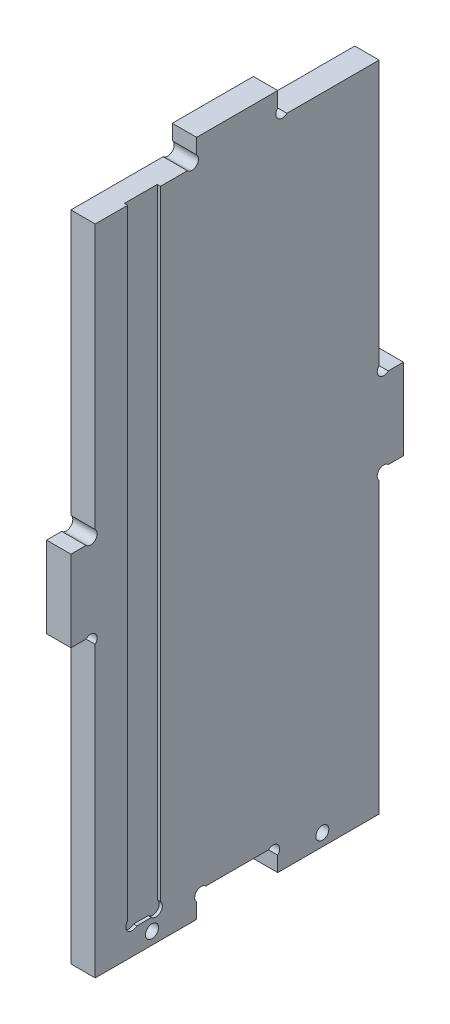
SolidWorks part; units mm, degrees
ref_plane "Plan de face" through (0, 0, 0) normal (0, 0, 1) x (1, 0, 0)
ref_plane "Plan de dessus" through (0, 0, 0) normal (0, 1, 0) x (1, 0, 0)
ref_plane "Plan de droite" through (0, 0, 0) normal (1, 0, 0) x (0, 0, -1)
sketch "Esquisse1" plane through (0, 0, 0) normal (1, 0, 0) x (0, 0, -1)
  line L0 (0, -30.7196) -> (0, 229.7017) construction
  line L1 (-9.0406, 0) -> (101.3462, 0) construction
  line L2 (-35.0297, 167) -> (123.1673, 167) construction
  line L3 (82, -30.7196) -> (82, 229.7017) construction
  line L4 (-35.0297, 6) -> (101.3462, 6) construction
  line L5 (-35.0297, 161) -> (101.3462, 161) construction
  line L6 (41, 198.0917) -> (41, -21.4572) construction
  line L7 (6, 213.5209) -> (6, -30.7196) construction
  line L8 (-35.0297, 83.5) -> (17.0365, 83.5) construction
  line L9 (17.0365, 73.5) -> (-35.0297, 73.5) construction
  line L10 (51, 181.2829) -> (51, 156.4029) construction
  line L11 (6, 73.5) -> (-20.8335, 46.6665) construction
  line L12 (3.7373, 73.5) -> (0, 73.5)
  line L13 (6, 71.2373) -> (6, 0)
  line L15 (3.7373, 93.5) -> (0, 93.5)
  line L16 (0, 93.5) -> (0, 73.5)
  line L17 (82, 93.5) -> (82, 73.5)
  line L18 (78.2627, 93.5) -> (82, 93.5)
  line L19 (78.2627, 73.5) -> (82, 73.5)
  line L20 (76, 189.4071) -> (76, -10.8473) construction
  line L21 (51, 163.2627) -> (51, 167)
  line L22 (51, 167) -> (31, 167)
  line L23 (31, 10.7132) -> (31, -21.4572) construction
  line L24 (31, 6) -> (49.7877, -12.7877) construction
  line L25 (-9.0406, 3) -> (23.2288, 3) construction
  line L26 (51, 161) -> (69.8431, 179.8431) construction
  line L27 (20, -21.4572) -> (20, 10.7132) construction
  line L28 (6, 0) -> (31, 0)
  line L29 (31, 0) -> (31, 3.7373)
  line L30 (33.2627, 6) -> (48.7373, 6)
  line L31 (51, 3.7373) -> (51, 0)
  line L32 (51, 0) -> (76, 0)
  line L33 (31, 167) -> (31, 163.2627)
  line L34 (28.7373, 161) -> (6, 161)
  line L35 (6, 161) -> (6, 95.7627)
  line L37 (53.2627, 161) -> (76, 161)
  line L45 (76, 71.2373) -> (76, 0)
  line L46 (76, 95.7627) -> (76, 161)
  arc A0 (76, 95.7627) -> (78.2627, 93.5) centre (77.1314, 94.6314) ccw
  arc A1 (6, 71.2373) -> (3.7373, 73.5) centre (4.8686, 72.3686) ccw
  arc A2 (6, 95.7627) -> (3.7373, 93.5) centre (4.8686, 94.6314) cw
  arc A3 (76, 71.2373) -> (78.2627, 73.5) centre (77.1314, 72.3686) cw
  arc A4 (51, 163.2627) -> (53.2627, 161) centre (52.1314, 162.1314) ccw
  arc A5 (31, 163.2627) -> (28.7373, 161) centre (29.8686, 162.1314) cw
  circle A6 centre (20, 3) radius 1.6
  arc A7 (33.2627, 6) -> (31, 3.7373) centre (32.1314, 4.8686) ccw
  arc A8 (48.7373, 6) -> (51, 3.7373) centre (49.8686, 4.8686) cw
  circle A9 centre (62, 3) radius 1.6
  dimension "D9" = 10
  dimension "D1" = 82
  dimension "D2" = 155
  dimension "D3" = 41
  dimension "D4" = 6
  dimension "D5" = 6
  dimension "D6" = 6
  dimension "D7" = 77.5
  dimension "D8" = 10
  dimension "D10" = 45
  dimension "D12" = 10
  dimension "D13" = 45
  dimension "D14" = 45
  dimension "D15" = 3
  dimension "D16" = 11
extrude "Boss.-Extru.1" add sketch "Esquisse1" along normal blind 6
sketch "Esquisse2" plane through (6, 0, 0) normal (-1, 0, 0) x (0, 0, 1)
  line L0 (-6, 190.4744) -> (-6, -14.3981) construction
  line L1 (-2.9516, 6) -> (-72.7833, 6) construction
  line L3 (-14, 216.2064) -> (-14, -14.3981) construction
  line L4 (-22.1, 216.2064) -> (-22.1, -14.3981) construction
  line L5 (-18.05, -5.7481) -> (-18.05, 5.2044) construction
  line L6 (-22.1, 165.8611) -> (-14, 165.8611)
  line L7 (-22.1, 165.8611) -> (-22.1, 8.2627)
  line L8 (-19.8373, 6) -> (-16.2627, 6)
  line L9 (-14, 165.8611) -> (-14, 8.2627)
  line L10 (-22.1, 6) -> (-13.9019, 14.1981) construction
  arc A0 (-22.1, 8.2627) -> (-19.8373, 6) centre (-20.9686, 7.1314) ccw
  arc A1 (-14, 8.2627) -> (-16.2627, 6) centre (-15.1314, 7.1314) cw
  dimension "D1" = 8
  dimension "D2" = 8.1
  dimension "D3" = 4.05
  dimension "D4" = 45
extrude "Enlèv. mat.-Extru.1" cut sketch "Esquisse2" along normal blind 0.8
